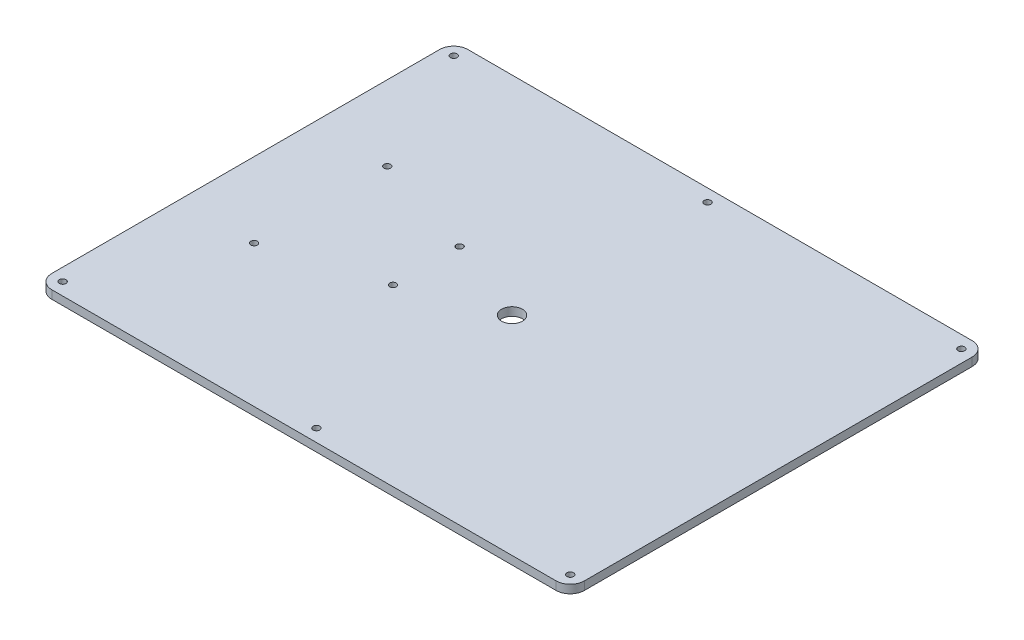
SolidWorks part; units mm, degrees
ref_plane "Front" through (0, 0, 0) normal (0, 0, 1) x (1, 0, 0)
ref_plane "Top" through (0, 0, 0) normal (0, 1, 0) x (1, 0, 0)
ref_plane "Right" through (0, 0, 0) normal (1, 0, 0) x (0, 0, -1)
sketch "Croquis1" plane through (0, 0, 0) normal (0, 1, 0) x (1, 0, 0)
  line L0 (0, 0) -> (50000, 0) construction
  line L1 (-303, 250) -> (303, 250)
  line L2 (-320, 233) -> (-320, -233)
  line L3 (-303, -250) -> (303, -250)
  line L4 (320, 233) -> (320, -233)
  line L5 (-320, 250) -> (320, -250) construction
  line L6 (-320, -250) -> (320, 250) construction
  line L7 (-305, -235) -> (305, -235) construction
  line L8 (-305, -235) -> (-305, 235) construction
  line L9 (-305, 235) -> (305, 235) construction
  line L10 (305, -235) -> (305, 235) construction
  line L11 (-305, -235) -> (305, 235) construction
  line L12 (-305, 235) -> (305, -235) construction
  line L13 (0, 0) -> (0, 50000) construction
  arc A0 (-320, -233) -> (-303, -250) centre (-303, -233) ccw
  arc A1 (320, -233) -> (303, -250) centre (303, -233) cw
  arc A2 (303, 250) -> (320, 233) centre (303, 233) cw
  arc A3 (-303, 250) -> (-320, 233) centre (-303, 233) ccw
  circle A4 centre (0, 235) radius 4
  circle A5 centre (305, 235) radius 4
  circle A6 centre (-305, 235) radius 4
  circle A7 centre (0, -235) radius 4
  circle A8 centre (305, -235) radius 4
  circle A9 centre (-305, -235) radius 4
  point P0 (0, 0)
  point P18 (0, 0)
  dimension "D3" = 17
  dimension "D6" = 8
  dimension "D1" = 640
  dimension "D2" = 500
  dimension "D4" = 15
  dimension "D5" = 15
extrude "Saliente-Extruir1" add sketch "Croquis1" along normal blind 10
sketch "Croquis2" plane through (0, 10, 0) normal (0, 1, 0) x (1, 0, 0)
  line L0 (0, 0) -> (-382.698, 0) construction
  line L1 (-320, 233) -> (-320, -233) construction
  circle A0 centre (-230, 80) radius 4
  circle A1 centre (-103, 40) radius 4
  circle A2 centre (0, 0) radius 12.5
  circle A3 centre (-103, -40) radius 4
  circle A4 centre (-230, -80) radius 4
  dimension "D1" = 8
  dimension "D4" = 127
  dimension "D6" = 25
  dimension "D2" = 160
  dimension "D3" = 80
  dimension "D5" = 90
extrude "Cortar-Extruir1" cut sketch "Croquis2" against normal blind 10
